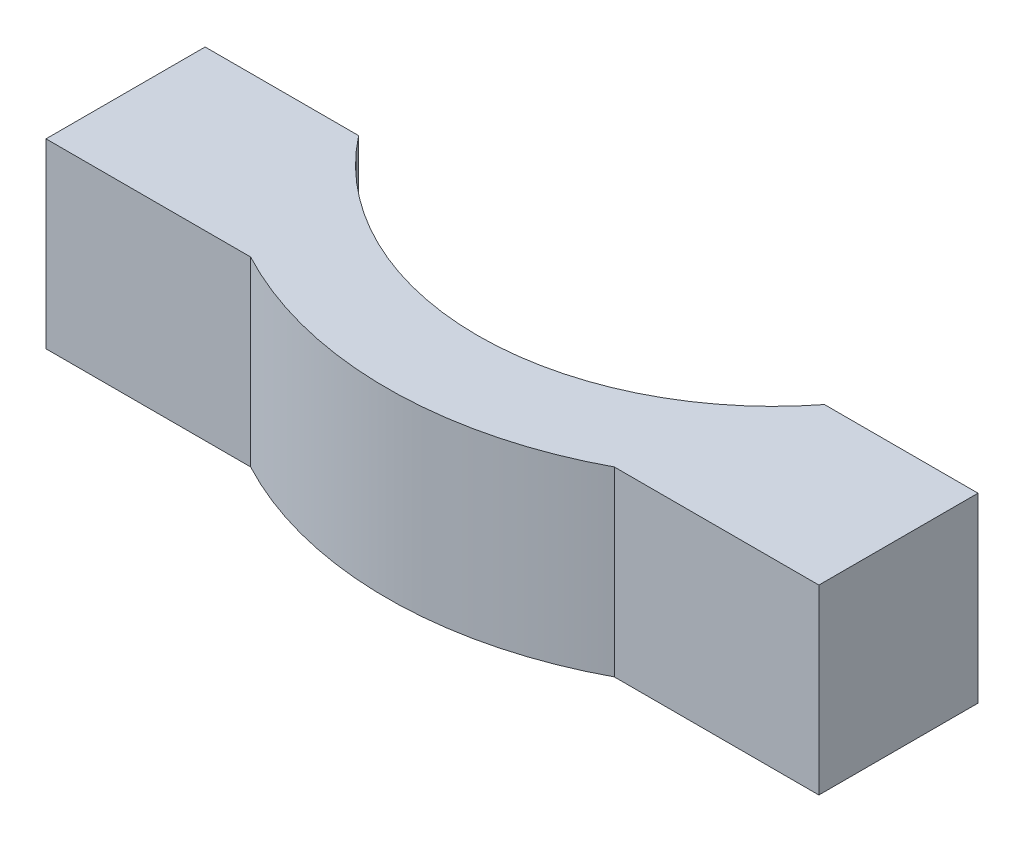
SolidWorks part; units mm, degrees
ref_plane "Front Plane" through (0, 0, 0) normal (0, 0, 1) x (1, 0, 0)
ref_plane "Top Plane" through (0, 0, 0) normal (0, 1, 0) x (1, 0, 0)
ref_plane "Right Plane" through (0, 0, 0) normal (1, 0, 0) x (0, 0, -1)
sketch "스케치3" plane through (0, 0, 0) normal (0, 1, 0) x (1, 0, 0)
  circle A0 centre (0, 0) radius 17
  dimension "D1" = 34
extrude "보스-돌출2" add sketch "스케치3" along normal blind 8
sketch "스케치6" plane through (0, 8, 0) normal (0, 1, 0) x (1, 0, 0)
  line L1 (-17, 0) -> (17, 0)
  line L2 (-17, 0) -> (-17, -15)
  line L3 (-17, -15) -> (17, -15)
  line L4 (17, 0) -> (17, -15)
  circle A0 centre (0, 0) radius 17 construction
  dimension "D1" = 15
extrude "보스-돌출3" add sketch "스케치6" against normal blind 8
sketch "스케치4" plane through (0, 8, 0) normal (0, 1, 0) x (1, 0, 0)
  line L0 (0, 0) -> (50000, 0) construction
  circle A0 centre (0, 0) radius 13
extrude "컷-돌출1" cut sketch "스케치4" against normal blind 8
sketch "스케치5" plane through (0, 8, 0) normal (0, 1, 0) x (1, 0, 0)
  line L0 (0, 0) -> (50000, 0) construction
  line L1 (-21.2309, -8) -> (49978.7691, -8) construction
  line L3 (-20.1034, -8) -> (19.1789, -8)
  line L4 (-20.1034, -8) -> (-20.1034, 18.0937)
  line L5 (-20.1034, 18.0937) -> (19.1789, 18.0937)
  line L6 (19.1789, -8) -> (19.1789, 18.0937)
  dimension "D1" = 8
extrude "컷-돌출2" cut sketch "스케치5" against normal blind 8
